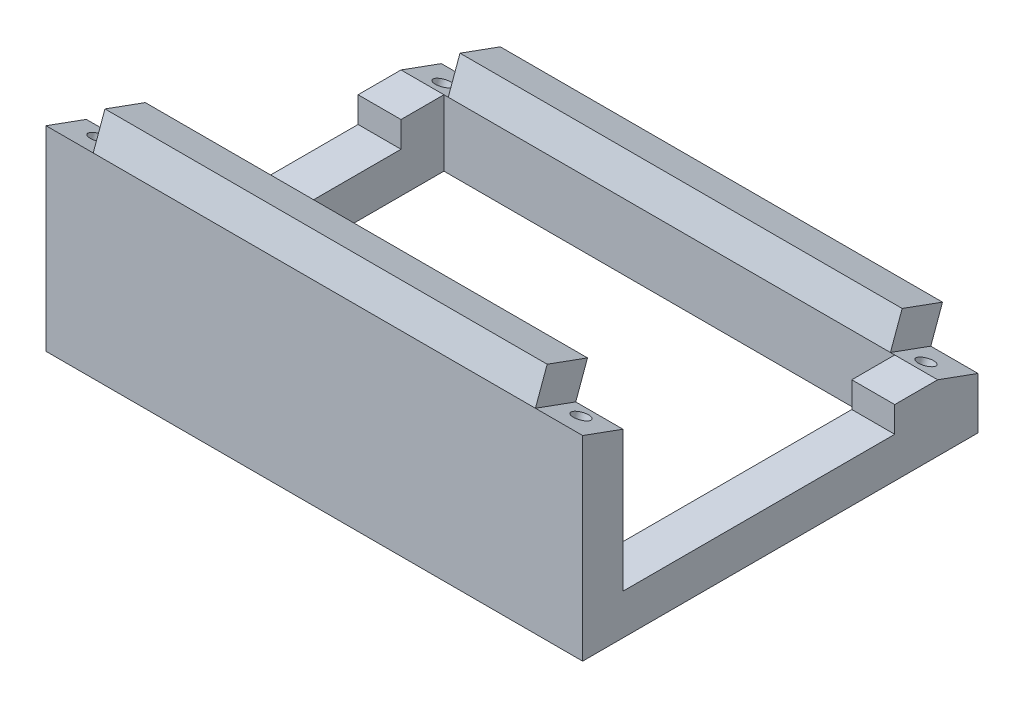
SolidWorks part; units mm, degrees
ref_plane "Front Plane" through (0, 0, 0) normal (0, 0, 1) x (1, 0, 0)
ref_plane "Top Plane" through (0, 0, 0) normal (0, 1, 0) x (1, 0, 0)
ref_plane "Right Plane" through (0, 0, 0) normal (1, 0, 0) x (0, 0, -1)
sketch "Sketch1" plane through (0, 0, 0) normal (1, 0, 0) x (0, 0, -1)
  line L0 (0, 0) -> (92.0899, 0)
  line L1 (92.0899, 0) -> (0, 33.518)
  line L2 (0, 33.518) -> (0, 0)
  dimension "D1" = 20
  dimension "D2" = 98
extrude "Boss-Extrude3" add sketch "Sketch1" against normal blind 125
sketch "Sketch3" plane through (0, 0, 0) normal (0, -1, 0) x (1, 0, 0)
  line L1 (0, -92.0899) -> (-125, -92.0899)
  line L2 (0, -92.0899) -> (0, 0)
  line L3 (0, 0) -> (-125, 0)
  line L4 (-125, -92.0899) -> (-125, 0)
  line L5 (0, -92.0899) -> (-125, 0) construction
  line L6 (0, 0) -> (-125, -92.0899) construction
  point P4 (-62.5, -46.0449)
extrude "Boss-Extrude5" add sketch "Sketch3" along normal blind 12
sketch "Sketch6" plane through (-125, 0, 0) normal (-1, 0, 0) x (0, 0, 1)
  line L0 (-92.0899, 0) -> (-82.693, 3.4202)
  line L1 (-92.0899, 0) -> (0, 33.518) construction
  line L2 (0, 33.518) -> (-9.3969, 30.0978)
  line L3 (-82.693, 3.4202) -> (-9.3969, 3.4202)
  line L4 (-9.3969, 3.4202) -> (-9.3969, 30.0978)
  line L5 (-82.693, 3.4202) -> (-9.3969, 30.0978)
  line M2 (0, 33.518) -> (-92.0899, 0)
  dimension "D1" = 10
  dimension "D2" = 10
extrude "Cut-Extrude1" cut sketch "Sketch6" against normal through all contours L3 L4 M2
sketch "Sketch7" plane through (0, 29.5971, -10.7725) normal (0, 0.9397, -0.342) x (1, 0, 0)
  line L0 (0, 76.5362) -> (-10, 76.5362)
  line L1 (0, 76.5362) -> (-125, 76.5362) construction
  line L2 (-125, 76.5362) -> (-115, 76.5362)
  line L3 (-125, 86.5362) -> (0, 86.5362) construction
  line L4 (-10, 76.5362) -> (-115, 76.5362)
  line L5 (-10, 76.5362) -> (-10, 86.5362)
  line L6 (-10, 86.5362) -> (-115, 86.5362)
  line L7 (-115, 76.5362) -> (-115, 86.5362)
  line L8 (-10, 76.5362) -> (-115, 86.5362) construction
  line L9 (-10, 86.5362) -> (-115, 76.5362) construction
  point P10 (-62.5, 81.5362)
  line M3 (-125, 76.5362) -> (0, 76.5362)
  line M5 (0, 86.5362) -> (-125, 86.5362)
  dimension "D1" = 10
  dimension "D2" = 10
extrude "Boss-Extrude6" add sketch "Sketch7" along normal blind 8 contours L7 L5 M3 M5
sketch "Sketch8" plane through (0, 29.5971, -10.7725) normal (0, 0.9397, -0.342) x (1, 0, 0)
  line L0 (0, -11.4638) -> (-10, -11.4638)
  line L1 (-125, -11.4638) -> (0, -11.4638) construction
  line L2 (-125, -11.4638) -> (-115, -11.4638)
  line L3 (0, -1.4638) -> (-125, -1.4638) construction
  line L4 (-10, -11.4638) -> (-115, -11.4638)
  line L5 (-10, -11.4638) -> (-10, -1.4638)
  line L6 (-10, -1.4638) -> (-115, -1.4638)
  line L7 (-115, -11.4638) -> (-115, -1.4638)
  line L8 (-10, -11.4638) -> (-115, -1.4638) construction
  line L9 (-10, -1.4638) -> (-115, -11.4638) construction
  point P10 (-62.5, -6.4638)
  line M3 (0, -1.4638) -> (-125, -1.4638)
  line M5 (-125, -11.4638) -> (0, -11.4638)
  dimension "D1" = 10
  dimension "D2" = 10
extrude "Boss-Extrude7" add sketch "Sketch8" along normal blind 8 contours L7 L5 M5 M3
sketch "Sketch9" plane through (0, 3.4202, 0) normal (0, 1, 0) x (1, 0, 0)
  line L0 (0, 82.693) -> (-10, 82.693)
  line L1 (-125, 82.693) -> (-115, 82.693)
  line L2 (0, 9.3969) -> (-125, 9.3969) construction
  line L3 (-10, 82.693) -> (-115, 82.693)
  line L4 (-10, 82.693) -> (-10, 9.3969)
  line L5 (-10, 9.3969) -> (-115, 9.3969)
  line L6 (-115, 82.693) -> (-115, 9.3969)
  line L7 (-10, 82.693) -> (-115, 9.3969) construction
  line L8 (-10, 9.3969) -> (-115, 82.693) construction
  point P10 (-62.5, 46.0449)
  line M2 (-125, 9.3969) -> (0, 9.3969)
  line M5 (-10, 82.693) -> (-115, 82.693)
extrude "Cut-Extrude2" cut sketch "Sketch9" against normal through all contours L6 L4 M5 M2
sketch "Sketch11" plane through (0, 3.4202, 0) normal (0, 1, 0) x (1, 0, 0)
  line L1 (0, 82.693) -> (-10, 82.693)
  line L2 (0, 82.693) -> (0, 9.3969)
  line L3 (0, 9.3969) -> (-10, 9.3969)
  line L4 (-10, 82.693) -> (-10, 9.3969)
  line L5 (0, 82.693) -> (-10, 9.3969) construction
  line L6 (0, 9.3969) -> (-10, 82.693) construction
  point P4 (-5, 46.0449)
extrude "Cut-Extrude3" cut sketch "Sketch11" against normal blind 6
sketch "Sketch12" plane through (0, 3.4202, 0) normal (0, 1, 0) x (1, 0, 0)
  line L1 (-115, 82.693) -> (-125, 82.693)
  line L2 (-115, 82.693) -> (-115, 9.3969)
  line L3 (-115, 9.3969) -> (-125, 9.3969)
  line L4 (-125, 82.693) -> (-125, 9.3969)
  line L5 (-115, 82.693) -> (-125, 9.3969) construction
  line L6 (-115, 9.3969) -> (-125, 82.693) construction
  point P4 (-120, 46.0449)
extrude "Cut-Extrude4" cut sketch "Sketch12" against normal blind 6
sketch "Sketch13" plane through (0, 0, -9.3969) normal (0, 0, -1) x (-1, 0, 0)
  line L1 (10, -2.5798) -> (115, -2.5798)
  line L2 (10, -2.5798) -> (10, 30.0978)
  line L3 (10, 30.0978) -> (115, 30.0978)
  line L4 (115, -2.5798) -> (115, 30.0978)
  line L5 (10, -2.5798) -> (115, 30.0978) construction
  line L6 (10, 30.0978) -> (115, -2.5798) construction
  point P4 (62.5, 13.759)
extrude "Cut-Extrude6" cut sketch "Sketch13" against normal blind 3
sketch "Sketch14" plane through (0, 29.5971, -10.7725) normal (0, 0.9397, -0.342) x (1, 0, 0)
  line L0 (0, 86.5362) -> (-6.25, 86.5362)
  line L1 (-10, 86.5362) -> (0, 86.5362) construction
  line L2 (-6.25, 86.5362) -> (-6.25, 80.2862)
  circle A0 centre (-6.25, 80.2862) radius 1.9
  dimension "D1" = 6.25
  dimension "D2" = 6.25
extrude "Cut-Extrude8" cut sketch "Sketch14" against normal blind 6
ref_plane "Plane1" through (-62.5, 0, 0) normal (1, 0, 0) x (0, 0, -1)
mirror "Mirror1" about plane through (-62.5, 0, 0) normal (1, 0, 0) of "Cut-Extrude8"
sketch "Sketch15" plane through (0, 29.5971, -10.7725) normal (0, 0.9397, -0.342) x (1, 0, 0)
  line L0 (0, -11.4638) -> (-6.25, -11.4638)
  line L1 (-10, -11.4638) -> (0, -11.4638) construction
  line L2 (-6.25, -11.4638) -> (-6.25, -5.2138)
  circle A0 centre (-6.25, -5.2138) radius 1.9
  dimension "D3" = 3.8
  dimension "D1" = 6.25
  dimension "D2" = 6.25
extrude "Cut-Extrude9" cut sketch "Sketch15" against normal blind 6
mirror "Mirror2" about plane through (-62.5, 0, 0) normal (1, 0, 0) of "Cut-Extrude9"
sketch "Sketch22" plane through (-10, 0, 0) normal (-1, 0, 0) x (0, 0, 1)
  line L0 (-9.3969, 30.0978) -> (-6.3969, 21.8553)
  line L1 (-6.3969, 30.0978) -> (-6.3969, -2.5798) construction
  line L2 (-6.3969, 21.8553) -> (-6.3969, 30.0978)
  line L3 (-6.3969, 30.0978) -> (-9.3969, 30.0978)
  line L4 (-12.1331, 37.6153) -> (-9.3969, 30.0978) construction
extrude "Boss-Extrude9" add sketch "Sketch22" along normal up to next
sketch "Sketch25" plane through (0, 0, -82.693) normal (0, 0, 1) x (1, 0, 0)
  line L1 (-10, -2.5798) -> (0, -2.5798)
  line L2 (-10, -2.5798) -> (-10, 3.4202)
  line L3 (-10, 3.4202) -> (0, 3.4202)
  line L4 (0, -2.5798) -> (0, 3.4202)
  line L5 (-10, -2.5798) -> (0, 3.4202) construction
  line L6 (-10, 3.4202) -> (0, -2.5798) construction
  line L7 (-125, -2.5798) -> (-115, -2.5798)
  line L8 (-125, -2.5798) -> (-125, 3.4202)
  line L9 (-125, 3.4202) -> (-115, 3.4202)
  line L10 (-115, -2.5798) -> (-115, 3.4202)
  line L11 (-125, -2.5798) -> (-115, 3.4202) construction
  line L12 (-125, 3.4202) -> (-115, -2.5798) construction
  point P4 (-5, 0.4202)
  point P11 (-120, 0.4202)
extrude "Boss-Extrude13" add sketch "Sketch25" along normal blind 10
sketch "Sketch26" plane through (-10, 0, 0) normal (1, 0, 0) x (0, 0, -1)
  line L0 (0, 33.518) -> (9.3969, 30.0978)
  line L1 (9.3969, 30.0978) -> (12.1331, 37.6153)
  line L2 (12.1331, 37.6153) -> (2.7362, 41.0355)
  line L3 (2.7362, 41.0355) -> (0, 33.518)
extrude "Cut-Extrude10" cut sketch "Sketch26" against normal blind 1
sketch "Sketch27" plane through (-10, 0, 0) normal (1, 0, 0) x (0, 0, -1)
  line L0 (82.693, 3.4202) -> (92.0899, 0)
  line L1 (92.0899, 0) -> (94.826, 7.5175)
  line L2 (94.826, 7.5175) -> (85.4291, 10.9377)
  line L3 (85.4291, 10.9377) -> (82.693, 3.4202)
extrude "Cut-Extrude11" cut sketch "Sketch27" against normal blind 1
mirror "Mirror3" about plane through (-62.5, 0, 0) normal (1, 0, 0) of "Cut-Extrude11", "Cut-Extrude10"
